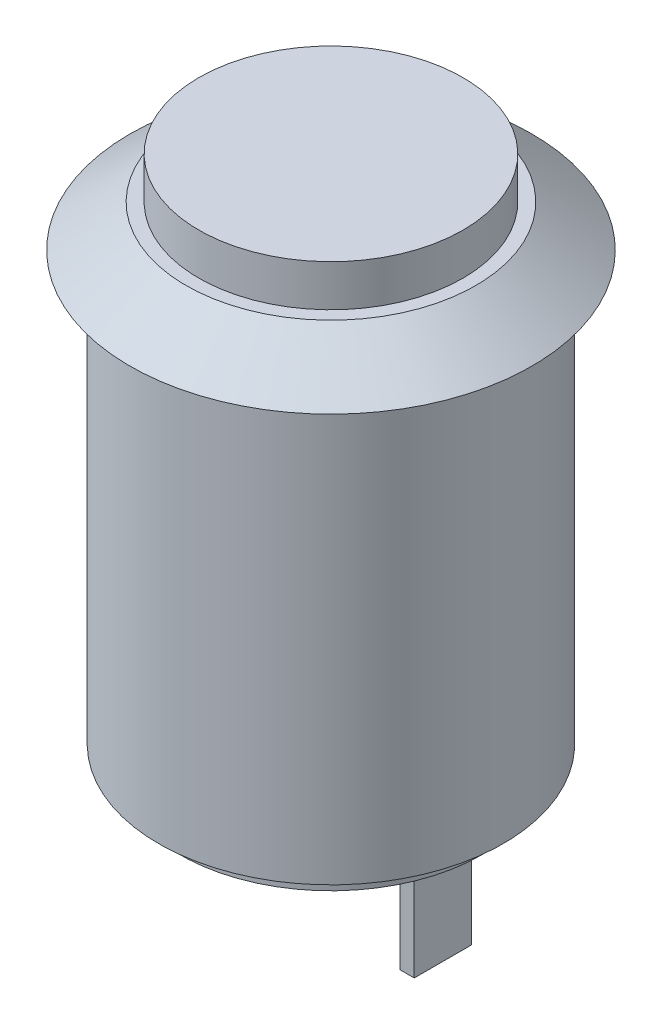
SolidWorks part; units mm, degrees
ref_plane "Front Plane" through (0, 0, 0) normal (0, 0, 1) x (1, 0, 0)
ref_plane "Top Plane" through (0, 0, 0) normal (0, 1, 0) x (1, 0, 0)
ref_plane "Right Plane" through (0, 0, 0) normal (1, 0, 0) x (0, 0, -1)
sketch "Sketch1" plane through (0, 0, 0) normal (0, 0, 1) x (1, 0, 0)
  line L0 (0, 0) -> (0, -13734.6034) construction
  line L1 (0, -14.9) -> (6, -14.9)
  line L2 (6, -14.9) -> (6, 0)
  line L3 (6, 0) -> (7, 0)
  line L4 (7, 0) -> (5.0433, 1.45)
  line L5 (5.0433, 1.45) -> (4.6, 1.45)
  line L6 (4.6, 1.45) -> (4.6, 2.9)
  line L7 (4.6, 2.9) -> (0, 2.9)
  line L8 (0, 2.9) -> (0, -14.9)
  line L9 (6, 0) -> (6, 1.45) construction
  point P7 (4.5, 5.1721)
  point P12 (5.6199, 1.45)
  point P14 (5.0433, 1.45)
  point P15 (6.5, 0)
  dimension "D1" = 2.9
  dimension "D2" = 9.2
  dimension "D3" = 12
  dimension "D4" = 14
  dimension "D5" = 14.9
revolve "Revolve1" add sketch "Sketch1" angle 360 about L8
sketch "Sketch2" plane through (0, -14.9, 0) normal (0, -1, 0) x (1, 0, 0)
  circle A0 centre (0, 0) radius 5.2641
extrude "Boss-Extrude1" add sketch "Sketch2" along normal blind 0.7
sketch "Sketch3" plane through (0, -15.6, 0) normal (0, -1, 0) x (1, 0, 0)
  line L0 (-3.65, 0) -> (3.65, 0) construction
  line L1 (-3.9, 1) -> (-3.4, 1)
  line L2 (-3.9, 1) -> (-3.9, -1)
  line L3 (-3.9, -1) -> (-3.4, -1)
  line L4 (-3.4, 1) -> (-3.4, -1)
  line L5 (-3.9, 1) -> (-3.4, -1) construction
  line L6 (-3.9, -1) -> (-3.4, 1) construction
  line L7 (3.4, 1) -> (3.9, 1)
  line L8 (3.4, 1) -> (3.4, -1)
  line L9 (3.4, -1) -> (3.9, -1)
  line L10 (3.9, 1) -> (3.9, -1)
  line L11 (3.4, 1) -> (3.9, -1) construction
  line L12 (3.4, -1) -> (3.9, 1) construction
  point P0 (-3.65, 0)
  point P5 (3.65, 0)
  point P12 (0, 0)
  dimension "D1" = 2
  dimension "D2" = 0.5
  dimension "D3" = 7.3
extrude "Boss-Extrude2" add sketch "Sketch3" along normal blind 3.9
